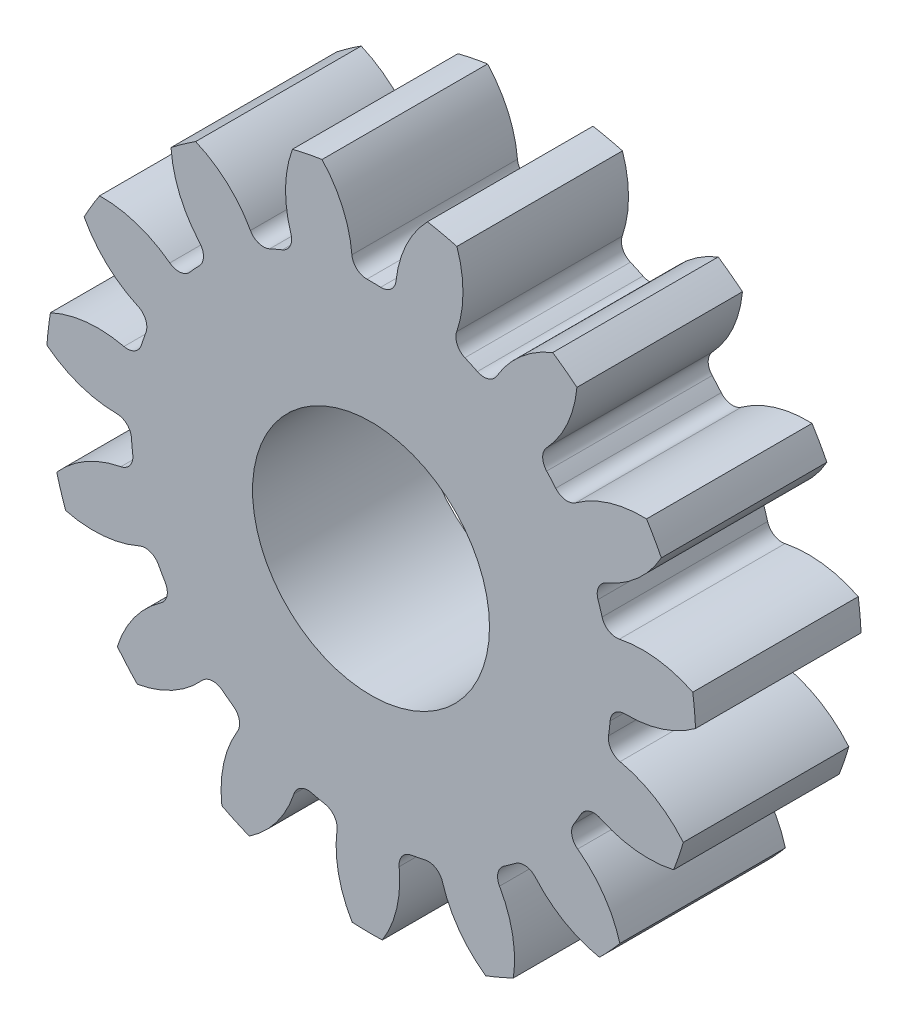
SolidWorks part; units mm, degrees
material "ABS"
ref_plane "Front" through (0, 0, 0) normal (0, 0, 1) x (1, 0, 0)
ref_plane "Top" through (0, 0, 0) normal (0, 1, 0) x (1, 0, 0)
ref_plane "Right" through (0, 0, 0) normal (1, 0, 0) x (0, 0, -1)
sketch "Sketch3" plane through (0, 0, 0) normal (0, 0, 1) x (1, 0, 0)
  circle A0 centre (0, 0) radius 21.59
  dimension "od" = 43.18
extrude "gearBody" add sketch "Sketch3" along normal blind 11
sketch "Sketch2" plane through (0, 0, 0) normal (0, 0, 1) x (1, 0, 0)
  line L0 (0, 0) -> (17.0393, 7.0579) construction
  line L1 (22.0105, -8.0941) -> (0, 0) construction
  line L2 (0, 0) -> (36.3143, 0) construction
  line L3 (19.0486, -0.229) -> (18.5878, -4.1711) construction
  line L5 (18.8182, -2.2) -> (0, 0) construction
  line L7 (0, 0) -> (18.4432, 0) construction
  arc A0 (18.4395, -0.3701) -> (18.0276, -3.8932) centre (0, 0) ccw construction
  arc A1 (21.5666, 1.0048) -> (20.7532, -5.9524) centre (0, 0) ccw construction
  arc A2 (19.0486, -0.229) -> (18.5878, -4.1711) centre (0, 0) ccw construction
  arc A3 (15.7838, -2.3046) -> (15.8898, -1.3984) centre (0, 0) ccw
  arc A4 (22.0105, -8.0941) -> (16.5506, -3.4102) centre (14.9518, -10.798) ccw
  arc A5 (22.0105, -8.0941) -> (23.2839, 2.7987) centre (0, 0) ccw
  arc A6 (23.2839, 2.7987) -> (16.8909, -0.4995) centre (17.0393, 7.0579) cw
  arc A7 (15.8898, -1.3984) -> (16.8909, -0.4995) centre (16.8715, -1.4848) cw
  arc A8 (16.5506, -3.4102) -> (15.7838, -2.3046) centre (16.759, -2.4469) cw
  point P6 (23.2839, 2.7987)
  point P22 (22.0105, -8.0941)
  dimension "baseDia" = 36.8864
  dimension "od" = 43.18
  dimension "pd" = 38.1
  dimension "rd" = 31.9024
  dimension "rFillet" = 0.9855
  dimension "pointX" = 23.2839
  dimension "pointY" = 2.7987
  dimension "CTT" = 3.9421
  dimension "flankCenterAngle" = 22.5
extrude "toothCut" cut sketch "Sketch2" along normal through all
pattern_circular "CirPattern1" count 15 over 360 about axis through (0, 0, 0) along (0, 0, 1) of "toothCut"
sketch "hub1Dia" plane through (0, 0, 0) normal (0, 0, -1) x (-1, 0, 0)
  circle A0 centre (0, 0) radius 12.7
  dimension "hub1Dia" = 25.4
sketch "hub2Dia" plane through (0, 0, 11) normal (0, 0, 1) x (1, 0, 0)
  circle A0 centre (0, 0) radius 12.7
  dimension "hub2dia" = 25.4
sketch "boreDia" plane through (0, 0, 0) normal (0, 0, 1) x (1, 0, 0)
  circle A0 centre (0, 0) radius 7.874
  dimension "boreDia" = 15.748
extrude "bore" cut sketch "boreDia" against normal mid plane 25400
